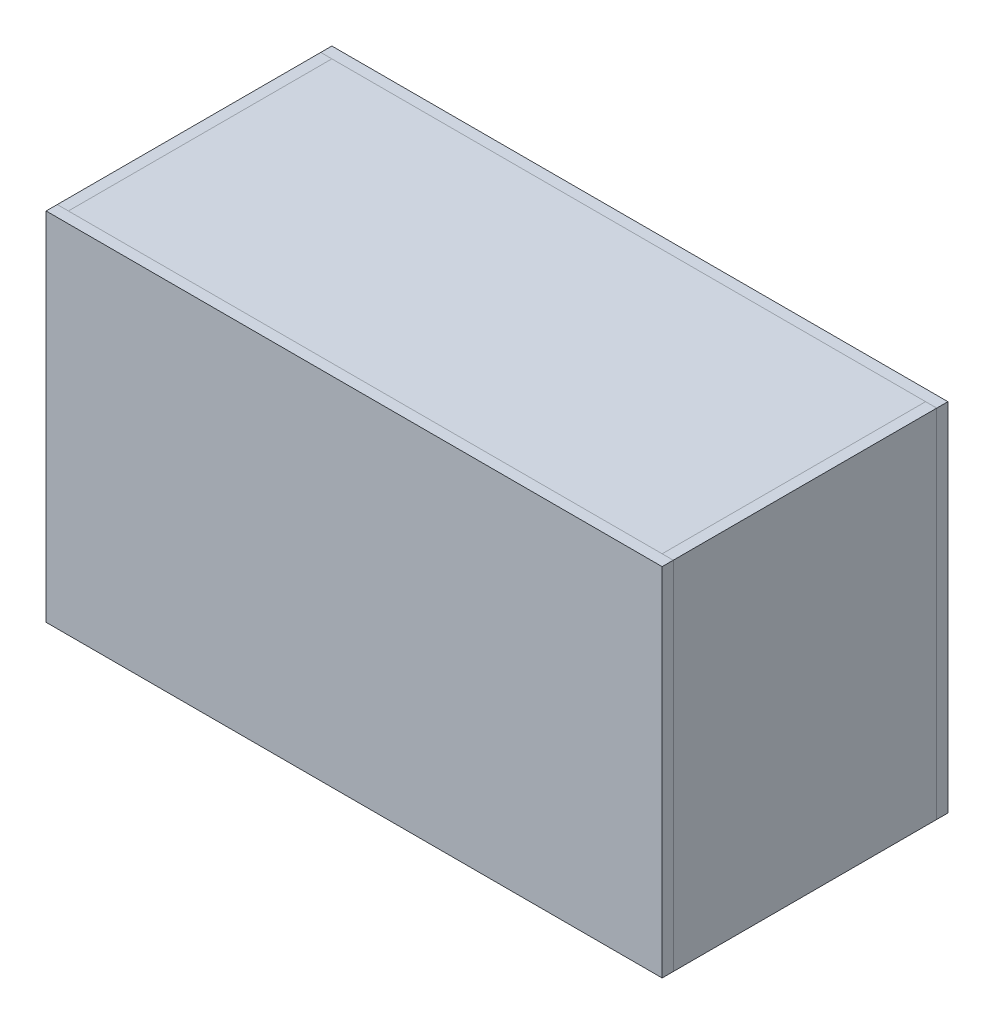
SolidWorks part; units mm, degrees
ref_plane "Front Plane" through (0, 0, 0) normal (0, 0, 1) x (1, 0, 0)
ref_plane "Top Plane" through (0, 0, 0) normal (0, 1, 0) x (1, 0, 0)
ref_plane "Right Plane" through (0, 0, 0) normal (1, 0, 0) x (0, 0, -1)
sketch "Sketch1" plane through (0, 0, 0) normal (0, 1, 0) x (1, 0, 0)
  line L1 (-508, -225.425) -> (508, -225.425)
  line L2 (-508, -225.425) -> (-508, 225.425)
  line L3 (-508, 225.425) -> (508, 225.425)
  line L4 (508, -225.425) -> (508, 225.425)
  line L5 (-508, -225.425) -> (508, 225.425) construction
  line L6 (-508, 225.425) -> (508, -225.425) construction
  point P0 (0, 0)
extrude "bottom" add sketch "Sketch1" against normal blind 19.05
sketch "Sketch2" plane through (-508, 0, 0) normal (-1, 0, 0) x (0, 0, 1)
  line L2 (225.425, -19.05) -> (-225.425, -19.05)
  line L3 (225.425, -19.05) -> (225.425, 590.55)
  line L4 (225.425, 590.55) -> (-225.425, 590.55)
  line L5 (-225.425, -19.05) -> (-225.425, 590.55)
extrude "side" add sketch "Sketch2" along normal blind 19.05 separate body contours L3 L2 L5 L4
mirror "Mirror4" about plane through (0, 0, 0) normal (1, 0, 0) of bodies 102
sketch "Sketch6" plane through (0, 0, 225.425) normal (0, 0, 1) x (1, 0, 0)
  line L1 (-527.05, 590.55) -> (527.05, 590.55)
  line L2 (-527.05, 590.55) -> (-527.05, -19.05)
  line L3 (-527.05, -19.05) -> (527.05, -19.05)
  line L4 (527.05, 590.55) -> (527.05, -19.05)
extrude "Boss-Extrude5" add sketch "Sketch6" along normal blind 19.05 separate body
mirror "Mirror5" about plane through (0, 0, 0) normal (0, 0, 1) of bodies 107
sketch "Sketch8" plane through (0, 590.55, 0) normal (0, 1, 0) x (1, 0, 0)
  line L1 (-508, 225.425) -> (508, 225.425)
  line L2 (-508, 225.425) -> (-508, -225.425)
  line L3 (-508, -225.425) -> (508, -225.425)
  line L4 (508, 225.425) -> (508, -225.425)
extrude "Boss-Extrude6" add sketch "Sketch8" against normal blind 19.05 separate body
